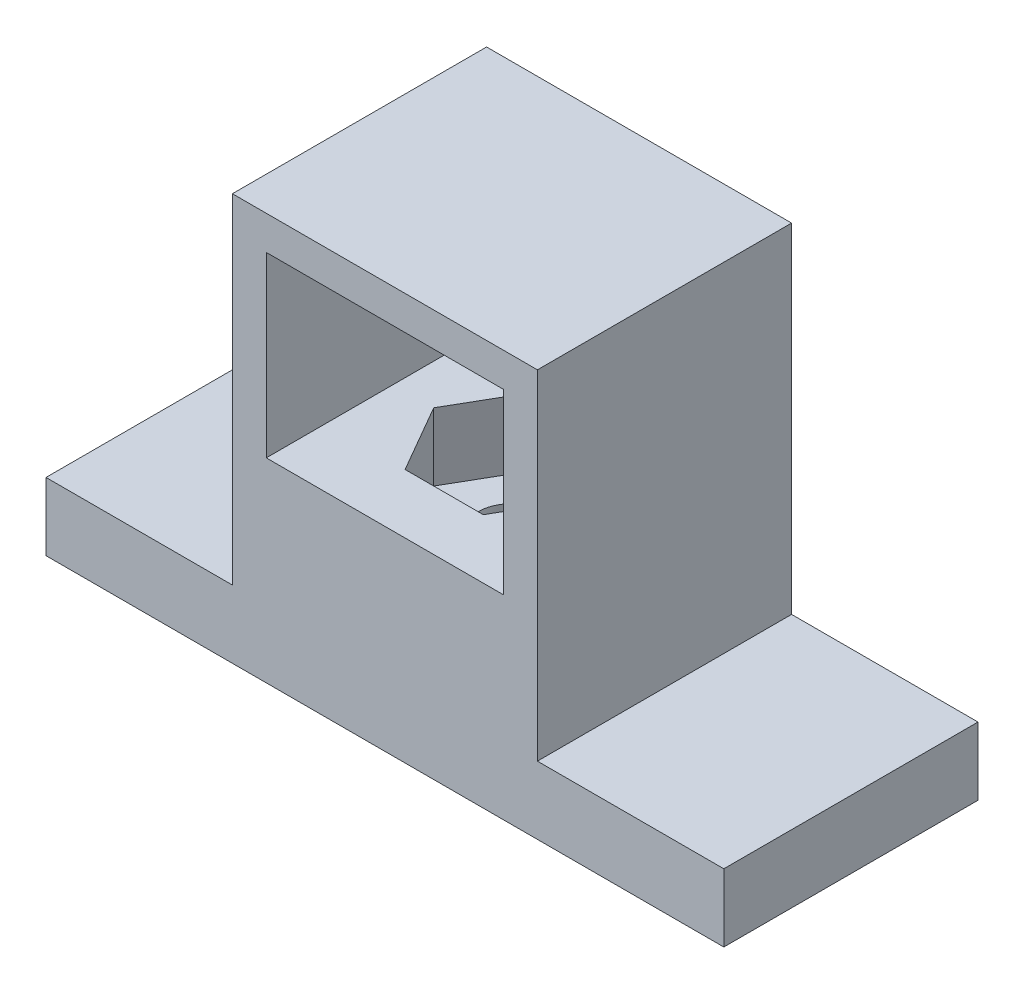
SolidWorks part; units mm, degrees
ref_plane "Front Plane" through (0, 0, 0) normal (0, 0, 1) x (1, 0, 0)
ref_plane "Top Plane" through (0, 0, 0) normal (0, 1, 0) x (1, 0, 0)
ref_plane "Right Plane" through (0, 0, 0) normal (1, 0, 0) x (0, 0, -1)
sketch "BaseSketch" plane through (0, 0, 0) normal (0, 1, 0) x (1, 0, 0)
  line L1 (-20, 7.5) -> (20, 7.5)
  line L2 (-20, 7.5) -> (-20, -7.5)
  line L3 (-20, -7.5) -> (20, -7.5)
  line L4 (20, 7.5) -> (20, -7.5)
  line L5 (-20, 7.5) -> (20, -7.5) construction
  line L6 (-20, -7.5) -> (20, 7.5) construction
  point P0 (0, 0)
  dimension "D1" = 40
  dimension "D2" = 15
extrude "Base" add sketch "BaseSketch" along normal blind 4
sketch "HolderSketch" plane through (0, 4, 0) normal (0, 1, 0) x (1, 0, 0)
  line L0 (-20, -7.5) -> (20, -7.5) construction
  line L1 (-9, 7.5) -> (9, 7.5)
  line L2 (-9, 7.5) -> (-9, -7.5)
  line L3 (-9, -7.5) -> (9, -7.5)
  line L4 (9, 7.5) -> (9, -7.5)
  line L5 (-9, 7.5) -> (9, -7.5) construction
  line L6 (-9, -7.5) -> (9, 7.5) construction
  point P0 (0, 0)
  dimension "D1" = 18
extrude "Holder" add sketch "HolderSketch" along normal blind 20
sketch "MotorCutSketch" plane through (0, 0, 7.5) normal (0, 0, 1) x (1, 0, 0)
  line L0 (0, 24) -> (0, 16.75) construction
  line L1 (-9, 24) -> (9, 24) construction
  line L2 (9, 24) -> (9, 4) construction
  line L3 (-7, 22) -> (7, 22)
  line L4 (-7, 22) -> (-7, 11.5)
  line L5 (-7, 11.5) -> (7, 11.5)
  line L6 (7, 22) -> (7, 11.5)
  line L7 (-7, 22) -> (7, 11.5) construction
  line L8 (-7, 11.5) -> (7, 22) construction
  dimension "D1" = 2
  dimension "D2" = 2
  dimension "D3" = 10.5
extrude "MotorCut" cut sketch "MotorCutSketch" against normal blind 19
sketch "NuttHoleSketch" plane through (0, 11.5, 0) normal (0, 1, 0) x (1, 0, 0)
  line L0 (-7, 7.5) -> (7, 7.5) construction
  line L1 (-2.3094, 4) -> (-4.6188, 0)
  line L2 (-4.6188, 0) -> (-2.3094, -4)
  line L3 (-2.3094, -4) -> (2.3094, -4)
  line L4 (2.3094, -4) -> (4.6188, 0)
  line L5 (4.6188, 0) -> (2.3094, 4)
  line L6 (2.3094, 4) -> (-2.3094, 4)
  circle A0 centre (0, 0) radius 4 construction
  dimension "D1" = 8
extrude "NuttHole" cut sketch "NuttHoleSketch" against normal blind 4
sketch "HoleSketch" plane through (0, 7.5, 0) normal (0, 1, 0) x (1, 0, 0)
  circle A0 centre (0, 0) radius 2
  dimension "D1" = 4
extrude "Cut-Extrude3" cut sketch "HoleSketch" against normal blind 64
